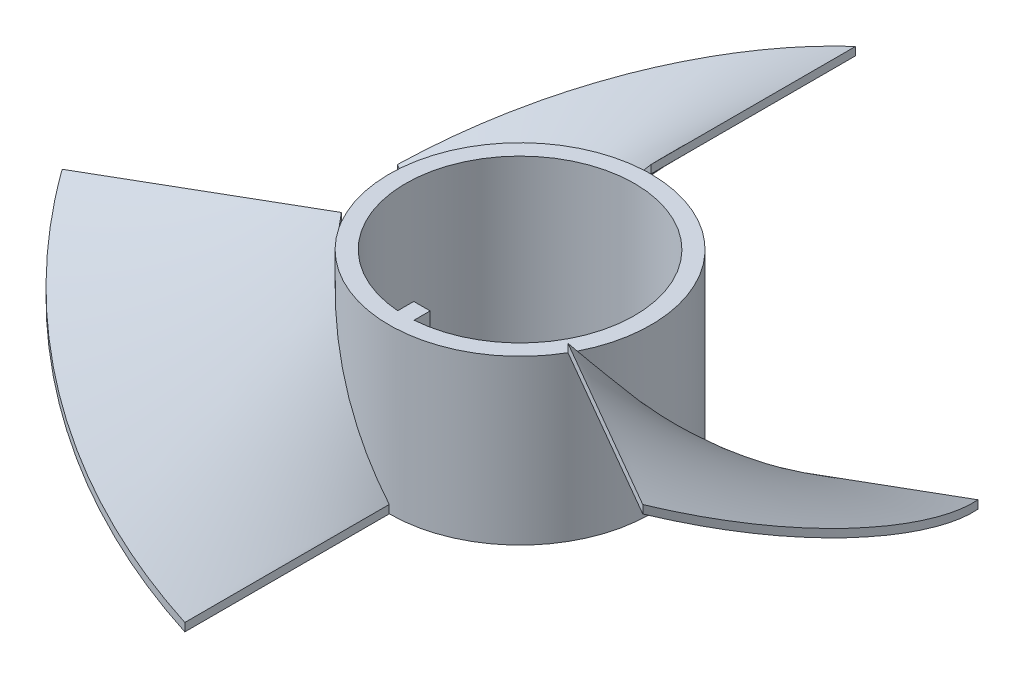
SolidWorks part; units mm, degrees
ref_plane "Front Plane" through (0, 0, 0) normal (0, 0, 1) x (1, 0, 0)
ref_plane "Top Plane" through (0, 0, 0) normal (0, 1, 0) x (1, 0, 0)
ref_plane "Right Plane" through (0, 0, 0) normal (1, 0, 0) x (0, 0, -1)
sketch "Sketch1" plane through (0, 0, 0) normal (0, 1, 0) x (1, 0, 0)
  line L0 (0, 0) -> (0, -14) construction
  line L1 (-1, -12) -> (1, -12)
  line L2 (-1, -12) -> (-1, -13.9642)
  line L3 (-1, -15) -> (0, -15)
  line L4 (1, -12) -> (1, -13.9642)
  line L5 (0, -16) -> (0, -32.298) construction
  line L6 (0, -14) -> (0, 0) construction
  line L7 (0, -15) -> (0, -16) construction
  arc A0 (1, -13.9642) -> (-1, -13.9642) centre (0, 0) ccw
  circle A1 centre (0, 0) radius 16
  circle A2 centre (0, 0) radius 14 construction
  dimension "D1" = 28
  dimension "D3" = 2
  dimension "D4" = 2
  dimension "D5" = 1
  dimension "D6" = 14
  dimension "D2" = 2
extrude "Boss-Extrude1" add sketch "Sketch1" along normal blind 20
sketch "Sketch2" plane through (0, 0, 0) normal (0, 1, 0) x (1, 0, 0)
  circle A0 centre (0, 0) radius 16 construction
  circle A1 centre (0, 0) radius 16
curve "Helix/Spiral1" pitch 120 height 20 turns 0.1667
sketch "Sketch3" plane through (0, 0, 0) normal (1, 0, 0) x (0, 0, -1)
  line L1 (-16, 0) -> (-41, 0)
  line L2 (-16, 0) -> (-16, 1)
  line L3 (-16, 1) -> (-41, 1)
  line L4 (-41, 0) -> (-41, 1)
  dimension "D1" = 1
  dimension "D2" = 25
sweep "Sweep1" add profiles "Sketch3" path "Helix/Spiral1"
ref_axis "Axis1" through (0, -1.1056, 0) along (0, 1, 0)
pattern_circular "CirPattern1" count 3 over 360 about axis through (0, -1.1056, 0) along (0, 1, 0) of "Sweep1"
